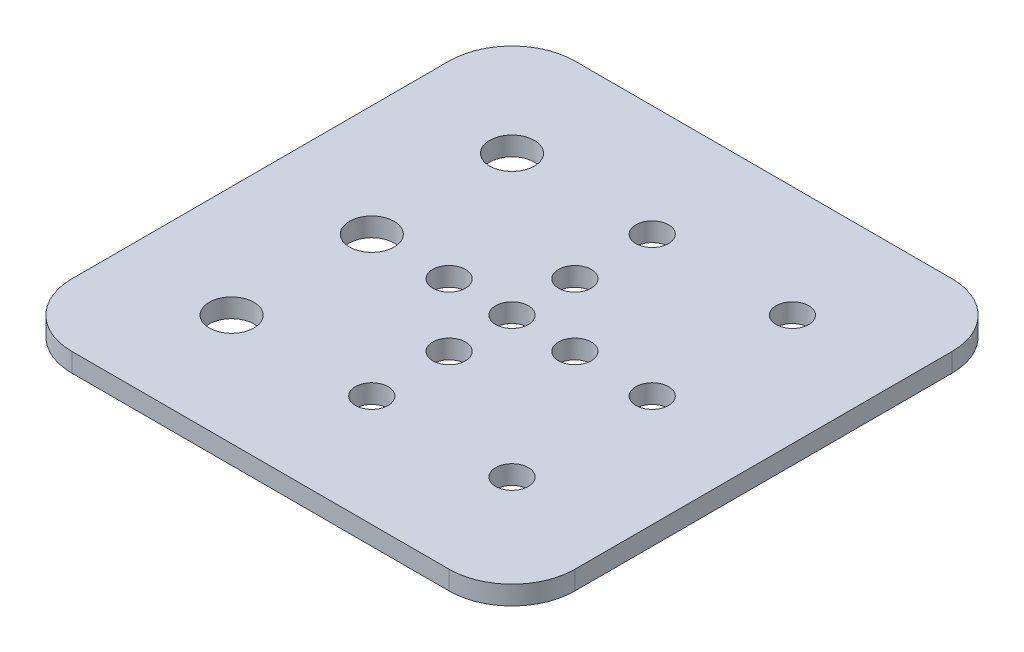
SolidWorks part; units mm, degrees
material "6061-T6 (SS)"
ref_plane "Front Plane" through (0, 0, 0) normal (0, 0, 1) x (1, 0, 0)
ref_plane "Top Plane" through (0, 0, 0) normal (0, 1, 0) x (1, 0, 0)
ref_plane "Right Plane" through (0, 0, 0) normal (1, 0, 0) x (0, 0, -1)
sketch "Sketch1" plane through (0, 0, 0) normal (0, 1, 0) x (1, 0, 0)
  line L0 (0, 0) -> (25.1102, 0) construction
  line L1 (30, -40) -> (-30, -40)
  line L2 (40, -30) -> (40, 30)
  line L3 (30, 40) -> (-30, 40)
  line L4 (-40, -30) -> (-40, 30)
  line L5 (40, -40) -> (-40, 40) construction
  line L6 (40, 40) -> (-40, -40) construction
  arc A0 (-30, -40) -> (-40, -30) centre (-30, -30) cw
  arc A1 (30, -40) -> (40, -30) centre (30, -30) ccw
  arc A2 (40, 30) -> (30, 40) centre (30, 30) ccw
  arc A3 (-30, 40) -> (-40, 30) centre (-30, 30) ccw
  circle A4 centre (0, 0) radius 2.6
  circle A5 centre (0, -10) radius 2.6
  circle A6 centre (-10, 0) radius 2.6
  circle A7 centre (10, 0) radius 2.6
  circle A8 centre (0, 10) radius 2.6
  circle A9 centre (-22.3, 22.3) radius 3.55
  circle A10 centre (-22.3, 0) radius 3.55
  circle A11 centre (-22.3, -22.3) radius 3.55
  circle A12 centre (0, 22.3) radius 2.6
  circle A13 centre (0, -22.3) radius 2.6
  circle A14 centre (22.3, 22.3) radius 2.6
  circle A15 centre (22.3, 0) radius 2.6
  circle A16 centre (22.3, -22.3) radius 2.6
  point P0 (0, 0)
  dimension "D2" = 10
  dimension "D3" = 5.2
  dimension "D5" = 7.1
  dimension "D1" = 80
  dimension "D4" = 10
  dimension "D6" = 44.6
  dimension "D7" = 44.6
  dimension "D8" = 17.7
extrude "Boss-Extrude1" add sketch "Sketch1" along normal blind 3
